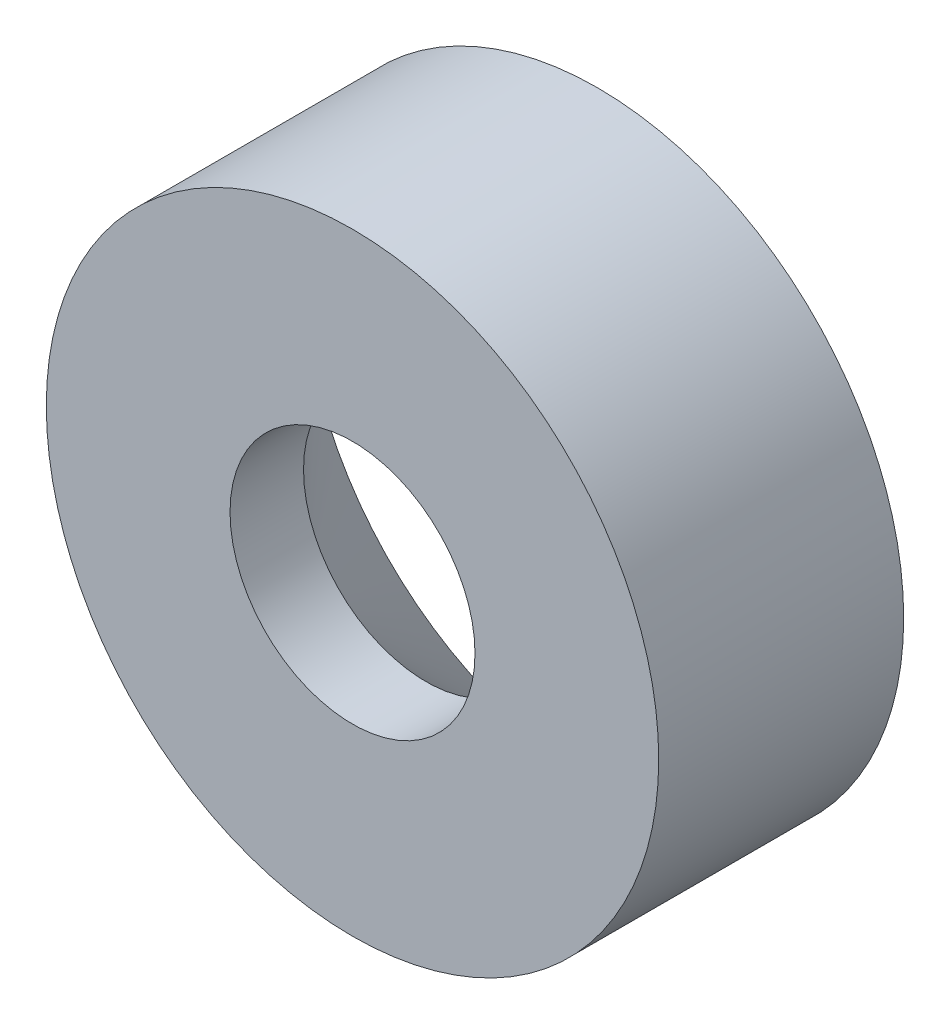
SolidWorks part; units mm, degrees
material "2024 合金"
ref_plane "正面" through (0, 0, 0) normal (0, 0, 1) x (1, 0, 0)
ref_plane "平面" through (0, 0, 0) normal (0, 1, 0) x (1, 0, 0)
ref_plane "右側面" through (0, 0, 0) normal (1, 0, 0) x (0, 0, -1)
sketch "ｽｹｯﾁ1" plane through (0, 0, 0) normal (0, 0, 1) x (1, 0, 0)
  circle A0 centre (0, 0) radius 12.5
  dimension "D1" = 25
extrude "ﾎﾞｽ - 押し出し1" add sketch "ｽｹｯﾁ1" along normal blind 10
sketch "ｽｹｯﾁ3" plane through (0, 0, 0) normal (0, 0, -1) x (-1, 0, 0)
  circle A0 centre (0, 0) radius 5
  dimension "D1" = 10
extrude "ｶｯﾄ - 押し出し1" cut sketch "ｽｹｯﾁ3" against normal through all
chamfer "面取り1" distance 7 angle 45 1 edges at (-5, 0, 0)
